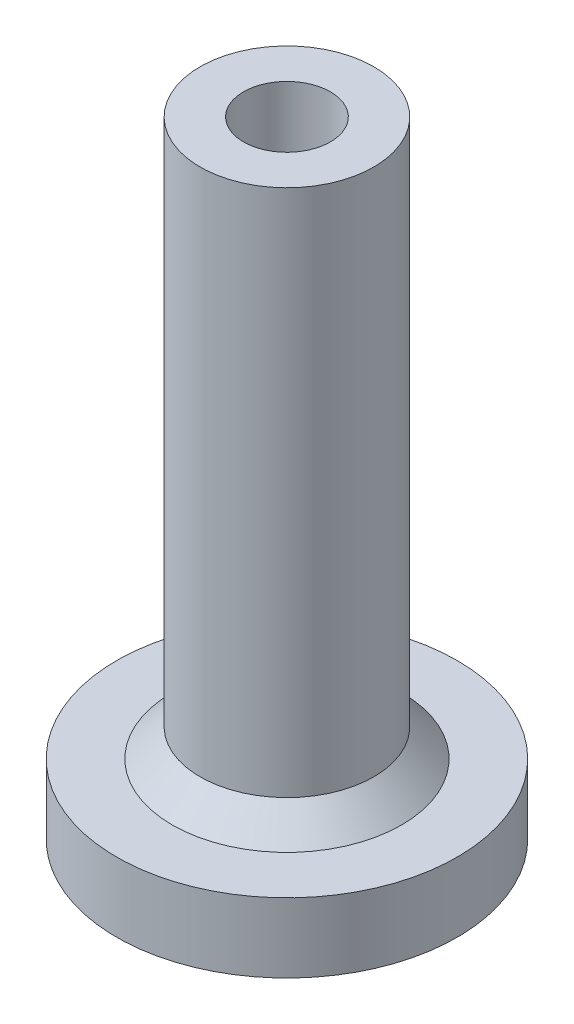
SolidWorks part; units mm, degrees
material "6061-T6 (SS)"
ref_plane "Front Plane" through (0, 0, 0) normal (0, 0, 1) x (1, 0, 0)
ref_plane "Top Plane" through (0, 0, 0) normal (0, 1, 0) x (1, 0, 0)
ref_plane "Right Plane" through (0, 0, 0) normal (1, 0, 0) x (0, 0, -1)
sketch "Sketch1" plane through (0, 0, 0) normal (0, 0, 1) x (1, 0, 0)
  line L0 (0, 0) -> (0, 15.3289) construction
  line L1 (-1.25, 0) -> (-1.25, 18)
  line L2 (-1.25, 18) -> (-2.5, 18)
  line L3 (-2.5, 18) -> (-2.5, 2.8)
  line L4 (-2.5, 2.8) -> (-3.3, 2)
  line L5 (-3.3, 2) -> (-4.9, 2)
  line L6 (-4.9, 2) -> (-4.9, 0)
  line L7 (-4.9, 0) -> (-1.25, 0)
  dimension "D1" = 2.5
  dimension "D2" = 16
  dimension "D3" = 2
  dimension "D4" = 0.8
  dimension "D5" = 45
  dimension "D6" = 5
  dimension "D7" = 9.8
revolve "Revolve1" add sketch "Sketch1" angle 360 about L0
